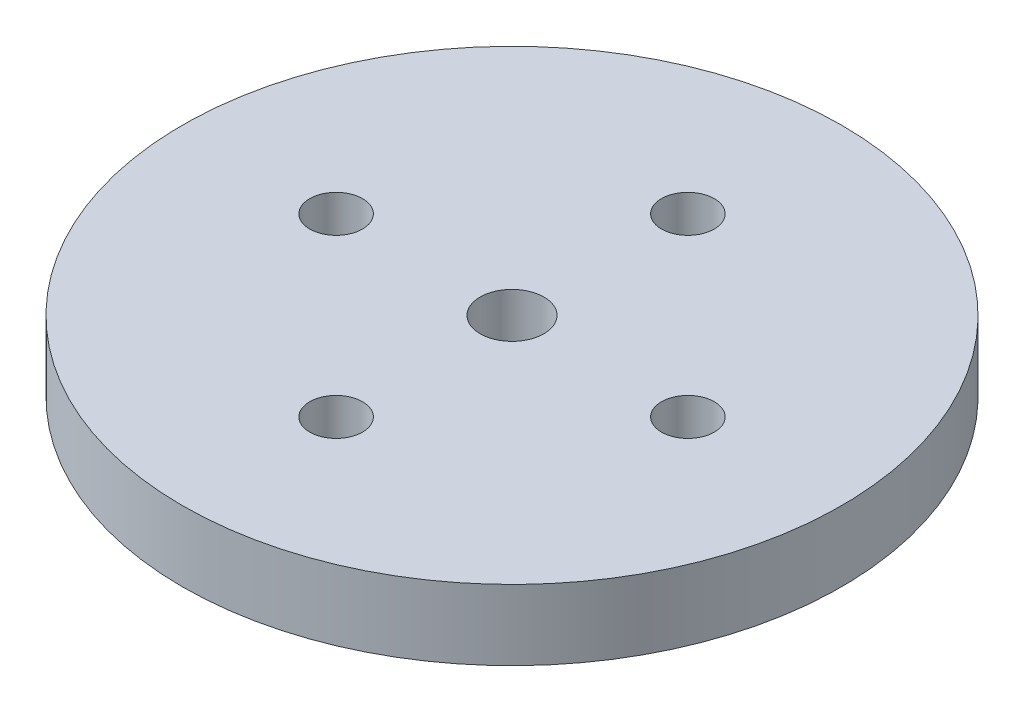
SolidWorks part; units mm, degrees
material "6063-T1"
ref_plane "Front Plane" through (0, 0, 0) normal (0, 0, 1) x (1, 0, 0)
ref_plane "Top Plane" through (0, 0, 0) normal (0, 1, 0) x (1, 0, 0)
ref_plane "Right Plane" through (0, 0, 0) normal (1, 0, 0) x (0, 0, -1)
sketch "Sketch1" plane through (0, 0, 0) normal (0, 1, 0) x (1, 0, 0)
  circle A0 centre (0, 0) radius 14.99
  circle A1 centre (0, 0) radius 1.45
  circle A2 centre (0, 8) radius 1.2
  circle A3 centre (8, 0) radius 1.2
  circle A4 centre (0, -8) radius 1.2
  circle A5 centre (-8, 0) radius 1.2
  point P15 (0, 0)
  dimension "D1" = 2.9
  dimension "D2" = 29.98
  dimension "D4" = 2.4
  dimension "D3" = 8
  dimension "D5" = 4
extrude "Boss-Extrude1" add sketch "Sketch1" along normal blind 3.2
